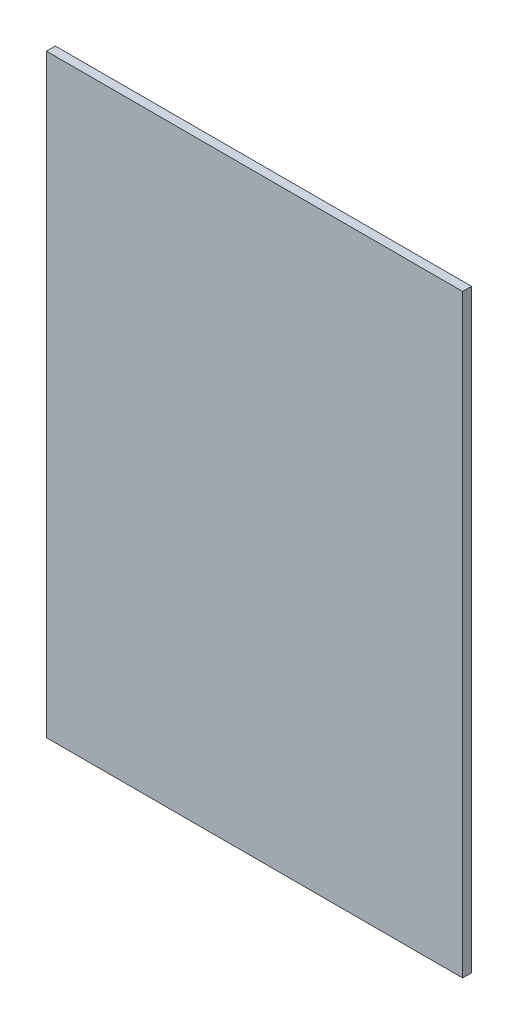
SolidWorks part; units mm, degrees
ref_plane "Front Plane" through (0, 0, 0) normal (0, 0, 1) x (1, 0, 0)
ref_plane "Top Plane" through (0, 0, 0) normal (0, 1, 0) x (1, 0, 0)
ref_plane "Right Plane" through (0, 0, 0) normal (1, 0, 0) x (0, 0, -1)
sketch "Sketch1" plane through (0, 0, 0) normal (0, 0, 1) x (1, 0, 0)
  line L1 (-700, -1000) -> (700, -1000)
  line L2 (-700, -1000) -> (-700, 1000)
  line L3 (-700, 1000) -> (700, 1000)
  line L4 (700, -1000) -> (700, 1000)
  line L5 (-700, -1000) -> (700, 1000) construction
  line L6 (-700, 1000) -> (700, -1000) construction
  point P0 (0, 0)
  dimension "D1" = 2000
  dimension "D2" = 1400
extrude "Boss-Extrude1" add sketch "Sketch1" along normal blind 30
